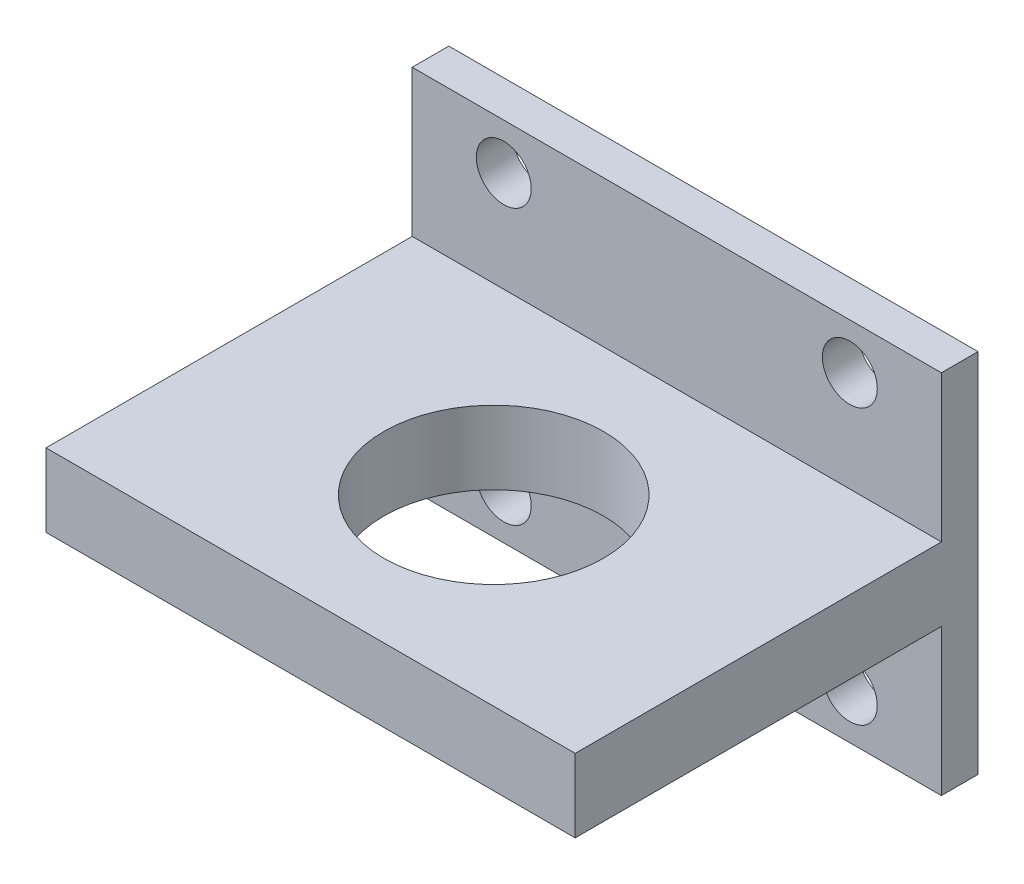
SolidWorks part; units mm, degrees
ref_plane "前视基准面" through (0, 0, 0) normal (0, 0, 1) x (1, 0, 0)
ref_plane "上视基准面" through (0, 0, 0) normal (0, 1, 0) x (1, 0, 0)
ref_plane "右视基准面" through (0, 0, 0) normal (1, 0, 0) x (0, 0, -1)
sketch "草图1" plane through (0, 0, 0) normal (0, 0, 1) x (1, 0, 0)
  line L0 (32.5883, 45.158) -> (3.6883, 45.158)
  line L1 (3.6883, 45.158) -> (3.6883, 25.158)
  line L2 (3.6883, 25.158) -> (32.5883, 25.158)
  line L3 (32.5883, 25.158) -> (32.5883, 45.158)
  line L4 (32.5883, 35.158) -> (27.5883, 35.158) construction
  line L5 (27.5883, 35.158) -> (27.5883, 42.658) construction
  line L6 (3.6883, 35.158) -> (32.5883, 35.158) construction
  line L7 (32.5883, 35.158) -> (18.1383, 35.158) construction
  line L8 (18.1383, 35.158) -> (18.1383, 45.158) construction
  circle A0 centre (27.5883, 42.658) radius 1.5
  circle A1 centre (8.6883, 42.658) radius 1.5
  circle A2 centre (8.6883, 27.658) radius 1.5
  circle A3 centre (27.5883, 27.658) radius 1.5
  dimension "D2" = 20
  dimension "D5" = 3
  dimension "D1" = 28.9
  dimension "D3" = 5
  dimension "D4" = 7.5
extrude "凸台-拉伸1" add sketch "草图1" along normal blind 2
sketch "草图2" plane through (0, 0, 2) normal (0, 0, 1) x (1, 0, 0)
  line L0 (3.6883, 35.158) -> (3.6883, 37.158)
  line L1 (3.6883, 45.158) -> (3.6883, 25.158) construction
  line L2 (3.6883, 37.158) -> (32.5883, 37.158)
  line L3 (32.5883, 25.158) -> (32.5883, 45.158) construction
  line L4 (32.5883, 37.158) -> (32.5883, 33.158)
  line L5 (32.5883, 33.158) -> (3.6883, 33.158)
  line L6 (3.6883, 33.158) -> (3.6883, 35.158)
  dimension "D1" = 2
  dimension "D2" = 4
extrude "凸台-拉伸2" add sketch "草图2" along normal blind 20
sketch "草图4" plane through (0, 33.158, 0) normal (0, -1, 0) x (1, 0, 0)
  line L0 (18.1383, 22) -> (18.1383, 2) construction
  line L1 (3.6883, 22) -> (32.5883, 22) construction
  line L2 (3.6883, 2) -> (32.5883, 2) construction
  circle A0 centre (18.1383, 12) radius 6
  dimension "D1" = 12
extrude "切除-拉伸1" cut sketch "草图4" against normal blind 10
